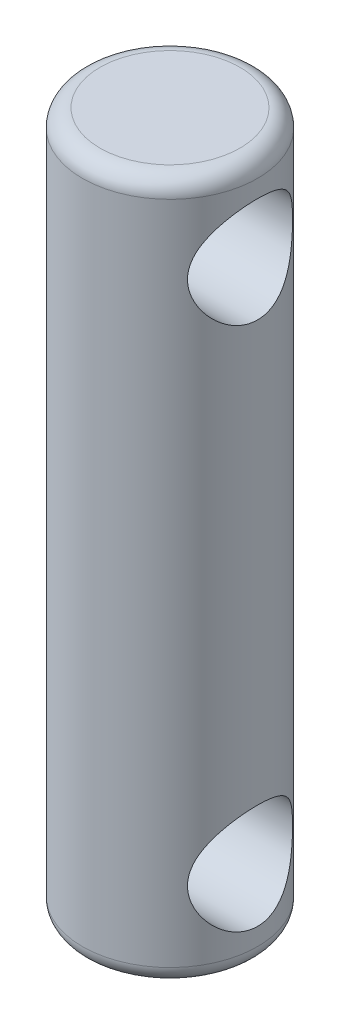
SolidWorks part; units mm, degrees
ref_plane "Front Plane" through (0, 0, 0) normal (0, 0, 1) x (1, 0, 0)
ref_plane "Top Plane" through (0, 0, 0) normal (0, 1, 0) x (1, 0, 0)
ref_plane "Right Plane" through (0, 0, 0) normal (1, 0, 0) x (0, 0, -1)
sketch "Sketch1" plane through (0, 0, 0) normal (0, 1, 0) x (1, 0, 0)
  circle A0 centre (0, 0) radius 2.5
  dimension "D1" = 5
extrude "Boss-Extrude1" add sketch "Sketch1" along normal blind 20
sketch "Sketch2" plane through (0, 0, 0) normal (1, 0, 0) x (0, 0, -1)
  line L0 (2.5, 20) -> (-2.5, 20) construction
  line L1 (0, 20) -> (0, 0) construction
  line L2 (-2.5, 0) -> (2.5, 0) construction
  circle A0 centre (0, 17.5) radius 1.5
  circle A1 centre (0, 2.5) radius 1.5
  point P11 (0, 0)
  dimension "D1" = 3
  dimension "D2" = 2.5
  dimension "D3" = 3
  dimension "D4" = 2.5
extrude "Cut-Extrude1" cut sketch "Sketch2" against normal mid plane 10
fillet "Fillet1" radius 0.5 2 edges at (0, 0, 2.5) (0, 20, 2.5)
